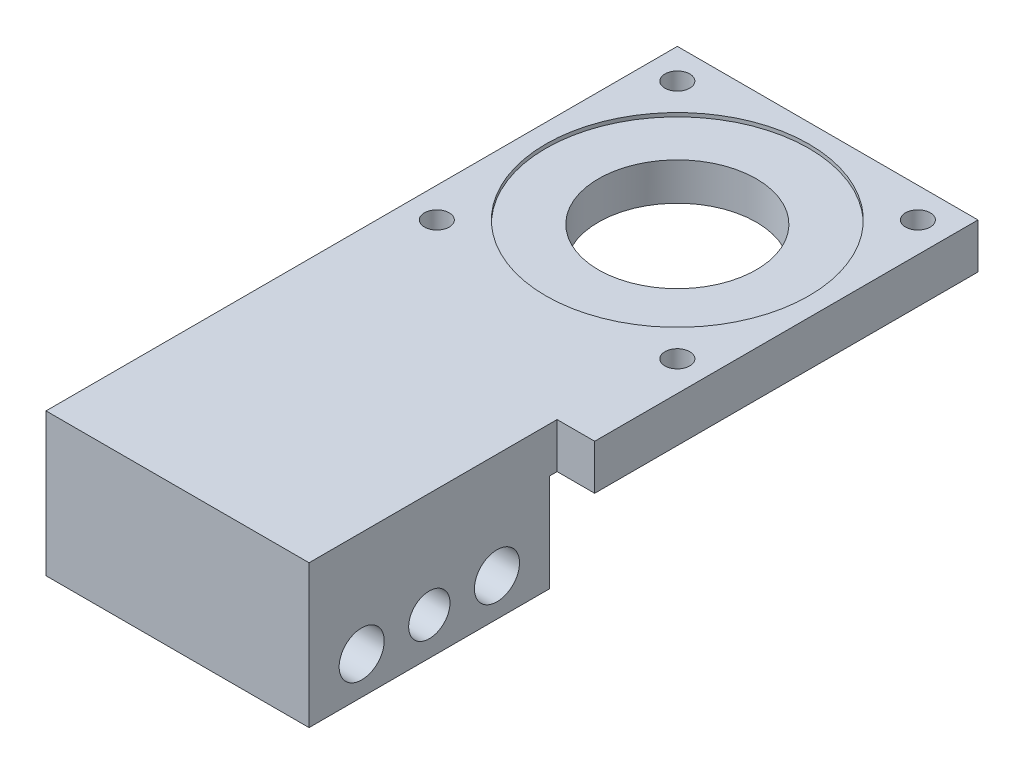
SolidWorks part; units mm, degrees
ref_plane "Front Plane" through (0, 0, 0) normal (0, 0, 1) x (1, 0, 0)
ref_plane "Top Plane" through (0, 0, 0) normal (0, 1, 0) x (1, 0, 0)
ref_plane "Right Plane" through (0, 0, 0) normal (1, 0, 0) x (0, 0, -1)
sketch "Sketch1" plane through (0, 0, 0) normal (0, 1, 0) x (1, 0, 0)
  line L0 (-20, 20) -> (-20, -64)
  line L1 (-16, -16) -> (16, -16) construction
  line L2 (-16, -16) -> (-16, 16) construction
  line L3 (-16, 16) -> (16, 16) construction
  line L4 (16, -16) -> (16, 16) construction
  line L5 (-16, -16) -> (16, 16) construction
  line L6 (-16, 16) -> (16, -16) construction
  line L7 (-20, -64) -> (20, -64)
  line L8 (20, -64) -> (20, 20)
  line L9 (20, 20) -> (-20, 20)
  line L10 (-20, -32) -> (20, -32) construction
  line L11 (-20, -60) -> (20, -60) construction
  line L12 (20, -54) -> (-20, -54) construction
  line L13 (-20, -50.5) -> (20, -50.5) construction
  line L14 (20, -45.5) -> (-20, -45.5) construction
  line L15 (-20, -36) -> (20, -36) construction
  line L16 (20, -42) -> (-20, -42) construction
  line L17 (0, -36) -> (0, -42) construction
  line L18 (0, -42) -> (0, -45.5) construction
  line L19 (0, -45.5) -> (0, -50.5) construction
  line L20 (0, -50.5) -> (0, -54) construction
  line L21 (0, -54) -> (0, -60) construction
  line L22 (0, -60) -> (0, -64) construction
  line L23 (0, -36) -> (0, -32) construction
  circle A0 centre (0, 0) radius 10.5
  circle A1 centre (-16, 16) radius 4 construction
  circle A3 centre (-16, 16) radius 2 construction
  circle A4 centre (0, 0) radius 17.5 construction
  point P0 (0, 0)
  point P37 (0, -39)
  point P38 (0, -57)
  point P39 (0, 20)
  dimension "D2" = 4
  dimension "D3" = 8
  dimension "D6" = 21
  dimension "D12" = 35
  dimension "D1" = 32
  dimension "D5" = 40
  dimension "D7" = 32
  dimension "D8" = 5
  dimension "D9" = 6
  dimension "D10" = 18
  dimension "D11" = 4
extrude "Boss-Extrude1" add sketch "Sketch1" along normal blind 6
sketch "Sketch2" plane through (0, 0, 0) normal (0, -1, 0) x (1, 0, 0)
  line L1 (-20, 64) -> (20, 64)
  line L2 (-20, 64) -> (-20, 32)
  line L3 (-20, 32) -> (20, 32)
  line L4 (20, 64) -> (20, 32)
extrude "Boss-Extrude2" add sketch "Sketch2" along normal blind 13
sketch "Sketch3" plane through (20, 0, 0) normal (1, 0, 0) x (0, 0, -1)
  line L0 (-57, -3) -> (-57, -13)
  line L2 (-32, -13) -> (-64, -13) construction
  line L3 (-48, -3) -> (-48, -13)
  line L4 (-39, -3) -> (-39, -13)
  line L5 (-64, 0) -> (20, 0) construction
  line L8 (-45.5, 0) -> (-50.5, 0) construction
  point P3 (-48, 0)
  dimension "D1" = 10
hole_wizard "Ø6.0mm Dowel Hole1" positions "Sketch4" profile "Sketch5" hole size "Ø6.0" standard "ANSI Metric" end condition through all
sketch "Sketch4" plane through (20, 0, 0) normal (1, 0, 0) x (0, 0, -1)
  line L0 (-57, -3) -> (-57, -13) construction
  line L1 (-39, -3) -> (-39, -13) construction
  point P0 (-57, -8)
  point P4 (-39, -8)
sketch "Sketch5" plane through (20, -8, 57) normal (0, 1, 0) x (0, 0, -1)
  line L0 (0, 0) -> (0, 40)
  line L1 (0, 40) -> (3, 40)
  line L2 (3, 40) -> (3, 0)
  line L5 (3, 0) -> (0, 0)
  line L11 (0, -6.35) -> (0, 107.95) construction
  dimension "Thru Hole Dia." = 6
  dimension "Thru Hole Depth" = 40
hole_wizard "M5 Clearance Hole1" positions "Sketch8" profile "Sketch9" hole size "M5" standard "ANSI Metric" end condition through all
sketch "Sketch8" plane through (-20, 0, 0) normal (-1, 0, 0) x (0, 0, 1)
  line L0 (48, -3) -> (48, -13) construction
  point P0 (48, -8)
sketch "Sketch9" plane through (-20, -8, 48) normal (0, 1, 0) x (0, 0, 1)
  line L0 (0, 0) -> (0, 40)
  line L1 (0, 40) -> (2.75, 40)
  line L2 (2.75, 40) -> (2.75, 0)
  line L5 (2.75, 0) -> (0, 0)
  line L11 (0, -6.35) -> (0, 107.95) construction
  dimension "Thru Hole Dia." = 5.5
  dimension "Thru Hole Depth" = 40
hole_wizard "M4x0.7 Tapped Hole1" positions "Sketch10" profile "Sketch11" tap size "M4x0.7" standard "ANSI Metric" end condition through all
sketch "Sketch10" plane through (0, 0, 0) normal (0, -1, 0) x (-1, 0, 0)
  point P0 (16, 16)
  point P3 (-16, 16)
  point P6 (-16, -16)
  point P9 (16, -16)
sketch "Sketch11" plane through (-16, 0, -16) normal (1, 0, 0) x (0, 0, -1)
  line L0 (0, 0) -> (0, 6)
  line L1 (0, 6) -> (1.65, 6)
  line L2 (1.65, 6) -> (1.65, 0)
  line L5 (1.65, 0) -> (0, 0)
  line L11 (0, -6.35) -> (0, 107.95) construction
  dimension "Thru Tap Drill Dia." = 3.3
  dimension "Thru Tap Drill Depth" = 6
sketch "Sketch12" plane through (0, 6, 0) normal (0, 1, 0) x (1, 0, 0)
  circle A0 centre (0, 0) radius 17.5
  dimension "D1" = 35
extrude "Cut-Extrude1" cut sketch "Sketch12" against normal blind 0.5
sketch "Sketch13" plane through (0, 0, 0) normal (0, -1, 0) x (1, 0, 0)
  circle A0 centre (0, 0) radius 17.5 construction
  circle A1 centre (0, 0) radius 17.5
extrude "Cut-Extrude2" cut sketch "Sketch13" against normal blind 0.5
sketch "Sketch14" plane through (20, 0, 0) normal (1, 0, 0) x (0, 0, -1)
  line L0 (-64, 6) -> (20, 6) construction
  line L1 (-64, -13) -> (-31, -13)
  line L2 (-64, -13) -> (-64, 6)
  line L3 (-64, 6) -> (-31, 6)
  line L4 (-31, -13) -> (-31, 6)
  line L5 (-32, -13) -> (-32, 0) construction
  dimension "D1" = 1
extrude "Cut-Extrude3" cut sketch "Sketch14" against normal blind 5
